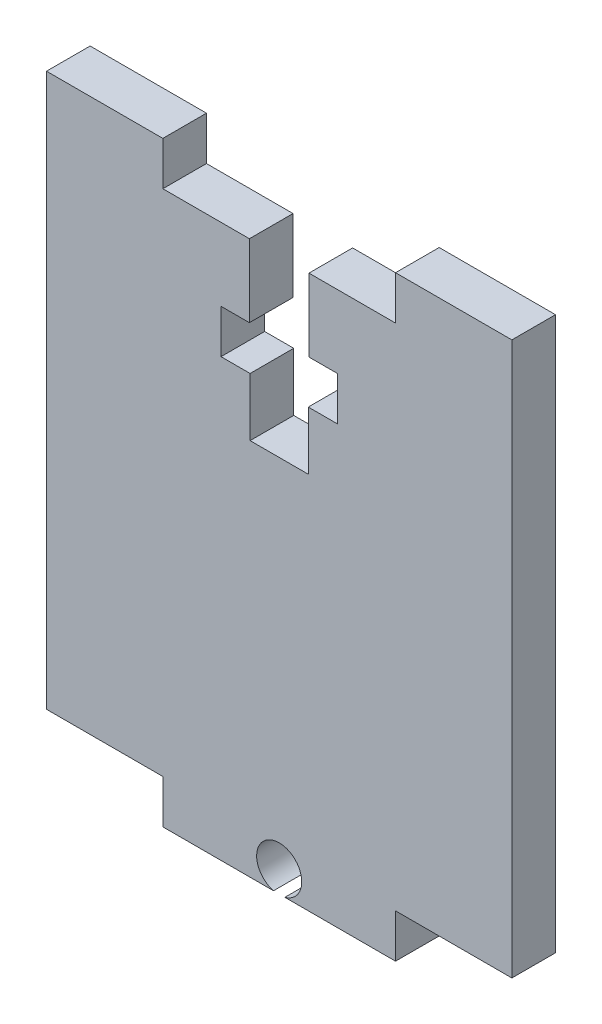
SolidWorks part; units mm, degrees
ref_plane "前视" through (0, 0, 0) normal (0, 0, 1) x (1, 0, 0)
ref_plane "上视" through (0, 0, 0) normal (0, 1, 0) x (1, 0, 0)
ref_plane "右视" through (0, 0, 0) normal (1, 0, 0) x (0, 0, -1)
sketch "草图2" plane through (0, 0, 0) normal (0, 0, 1) x (1, 0, 0)
  line L0 (0, 103.0974) -> (0, -63.3868) construction
  line L1 (2.0479, 48.8553) -> (8, 48.8553)
  line L2 (8, 48.8553) -> (8, 51.8553)
  line L3 (8, 51.8553) -> (16, 51.8553)
  line L4 (16, 51.8553) -> (16, 13.8553)
  line L5 (16, 13.8553) -> (8, 13.8553)
  line L6 (2.0479, 48.8553) -> (2.0479, 43.8553)
  line L7 (2.0479, 43.8553) -> (4, 43.8553)
  line L8 (4, 43.8553) -> (4, 40.8553)
  line L9 (4, 40.8553) -> (2, 40.8553)
  line L10 (2, 40.8553) -> (2, 36.8553)
  line L11 (2, 36.8553) -> (-2, 36.8553)
  line L12 (-8, 10.8553) -> (-0.3905, 10.8553)
  line L13 (8, 10.8553) -> (8, 13.8553)
  line L14 (-8, 10.8553) -> (-8, 13.8553)
  line L15 (0.3905, 10.8553) -> (8, 10.8553)
  line L16 (-2, 40.8553) -> (-2, 36.8553)
  line L17 (-4, 40.8553) -> (-2, 40.8553)
  line L18 (-4, 43.8553) -> (-4, 40.8553)
  line L19 (-2.0479, 43.8553) -> (-4, 43.8553)
  line L20 (-2.0479, 48.8553) -> (-2.0479, 43.8553)
  line L21 (-16, 13.8553) -> (-8, 13.8553)
  line L22 (-16, 51.8553) -> (-16, 13.8553)
  line L23 (-8, 51.8553) -> (-16, 51.8553)
  line L24 (-8, 48.8553) -> (-8, 51.8553)
  line L25 (-2.0479, 48.8553) -> (-8, 48.8553)
  arc A0 (0.3905, 10.8553) -> (-0.3905, 10.8553) centre (0, 12.3553) ccw
  point P22 (0, 36.8553)
  dimension "D12" = 1.5
  dimension "D11" = 3.1
  dimension "D1" = 8
  dimension "D2" = 8
  dimension "D3" = 3
  dimension "D4" = 12
  dimension "D5" = 5
  dimension "D6" = 3
  dimension "D7" = 2
  dimension "D8" = 2
  dimension "D9" = 35
  dimension "D10" = 3
extrude "凸台-拉伸1" add sketch "草图2" along normal blind 3
